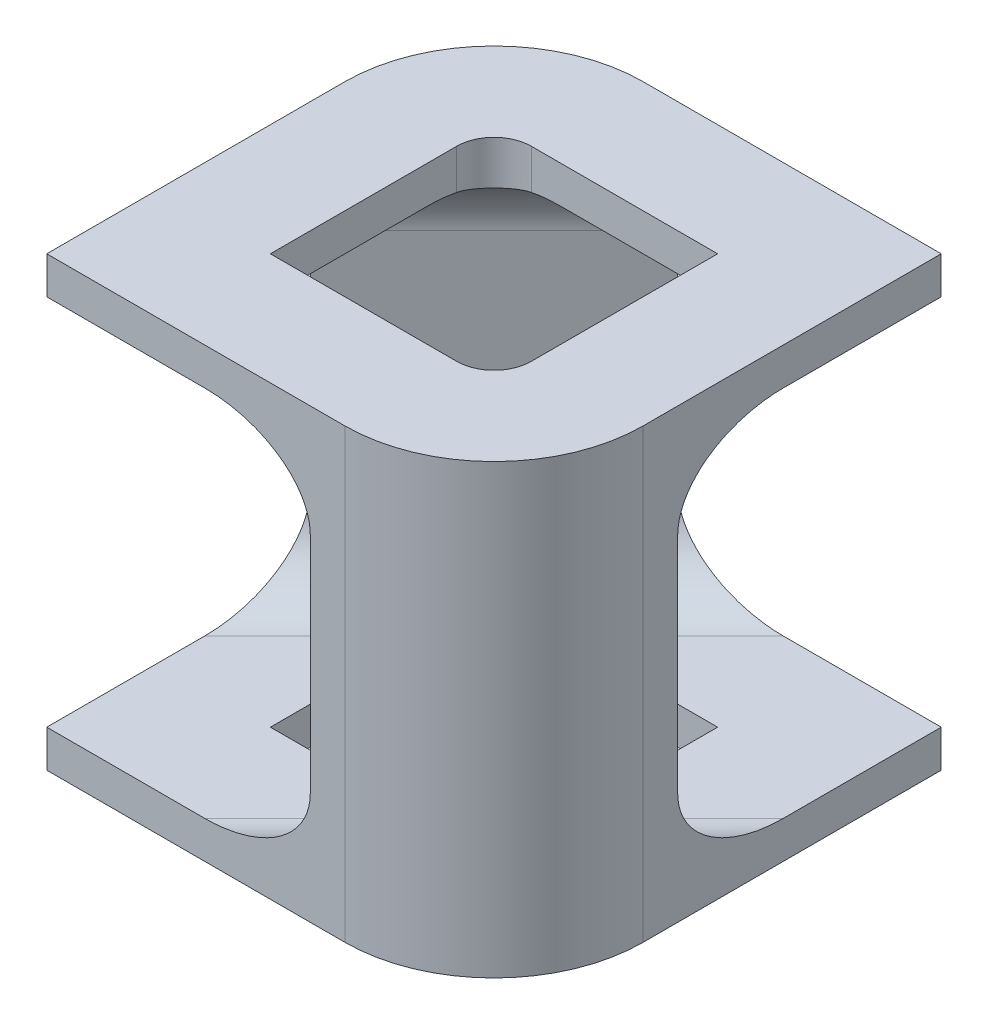
SolidWorks part; units mm, degrees
ref_plane "Front Plane" through (0, 0, 0) normal (0, 0, 1) x (1, 0, 0)
ref_plane "Top Plane" through (0, 0, 0) normal (0, 1, 0) x (1, 0, 0)
ref_plane "Right Plane" through (0, 0, 0) normal (1, 0, 0) x (0, 0, -1)
sketch "Sketch1" plane through (0, 0, 0) normal (0, 1, 0) x (1, 0, 0)
  line L1 (0, 0) -> (50.8, 0)
  line L2 (0, 0) -> (0, 50.8)
  line L3 (25.4, 76.2) -> (76.2, 76.2)
  line L4 (76.2, 25.4) -> (76.2, 76.2)
  line L5 (19.05, 19.05) -> (50.8, 19.05)
  line L6 (19.05, 19.05) -> (19.05, 50.8)
  line L7 (25.4, 57.15) -> (57.15, 57.15)
  line L8 (57.15, 25.4) -> (57.15, 57.15)
  arc A0 (50.8, 0) -> (76.2, 25.4) centre (50.8, 25.4) ccw
  arc A1 (0, 50.8) -> (25.4, 76.2) centre (25.4, 50.8) cw
  arc A2 (50.8, 19.05) -> (57.15, 25.4) centre (50.8, 25.4) ccw
  arc A3 (19.05, 50.8) -> (25.4, 57.15) centre (25.4, 50.8) cw
  point P7 (76.2, 0)
  point P10 (0, 76.2)
  dimension "D3" = 25.4
  dimension "D8" = 6.35
  dimension "D1" = 76.2
  dimension "D2" = 76.2
  dimension "D4" = 19.05
  dimension "D5" = 19.05
  dimension "D6" = 19.05
  dimension "D7" = 19.05
extrude "Boss-Extrude1" add sketch "Sketch1" along normal blind 76.2
sketch "Sketch2" plane through (0, 0, 0) normal (0, 0, 1) x (1, 0, 0)
  line L6 (46.8533, 5.718) -> (46.8533, 0)
  line L7 (0, 0) -> (50.8, 0) construction
  line L8 (46.8533, 0) -> (46.8533, 76.2)
  line L9 (0, 76.2) -> (50.8, 76.2) construction
ref_plane "Plane2" through (25.4, 0, -25.4) normal (-0.7071, 0, 0.7071) x (0.7071, 0, 0.7071)
sketch "Sketch3" plane through (25.4, 0, -25.4) normal (-0.7071, 0, 0.7071) x (0.7071, 0, 0.7071)
  line L0 (0, 38.1) -> (39.7663, 38.1) construction
  line L1 (0, 76.2) -> (0, 0) construction
  line L2 (-31.75, 38.1) -> (-31.75, 19.05)
  line L3 (0, 38.1) -> (31.75, 38.1) construction
  line L4 (0, 38.1) -> (0, 69.85) construction
  line L5 (-19.05, 69.85) -> (19.05, 69.85)
  line L6 (31.75, 38.1) -> (31.75, 57.15)
  line L8 (31.75, 38.1) -> (31.75, 19.05)
  line L9 (19.05, 6.35) -> (-19.05, 6.35)
  line L10 (0, 38.1) -> (0, 6.35) construction
  line L11 (-31.75, 38.1) -> (-31.75, 57.15)
  arc A0 (31.75, 19.05) -> (19.05, 6.35) centre (19.05, 19.05) cw
  arc A1 (19.05, 69.85) -> (31.75, 57.15) centre (19.05, 57.15) cw
  arc A2 (-31.75, 19.05) -> (-19.05, 6.35) centre (-19.05, 19.05) ccw
  arc A3 (-19.05, 69.85) -> (-31.75, 57.15) centre (-19.05, 57.15) ccw
  point P13 (31.75, 69.85)
  dimension "D4" = 12.7
  dimension "D1" = 31.75
  dimension "D2" = 31.75
  dimension "D3" = 31.75
extrude "Cut-Extrude4" cut sketch "Sketch3" against normal blind 82.042 and the other way blind 50.546 contours L8 A0 L9 A2 L2 L11 A3 L5 A1 L6
